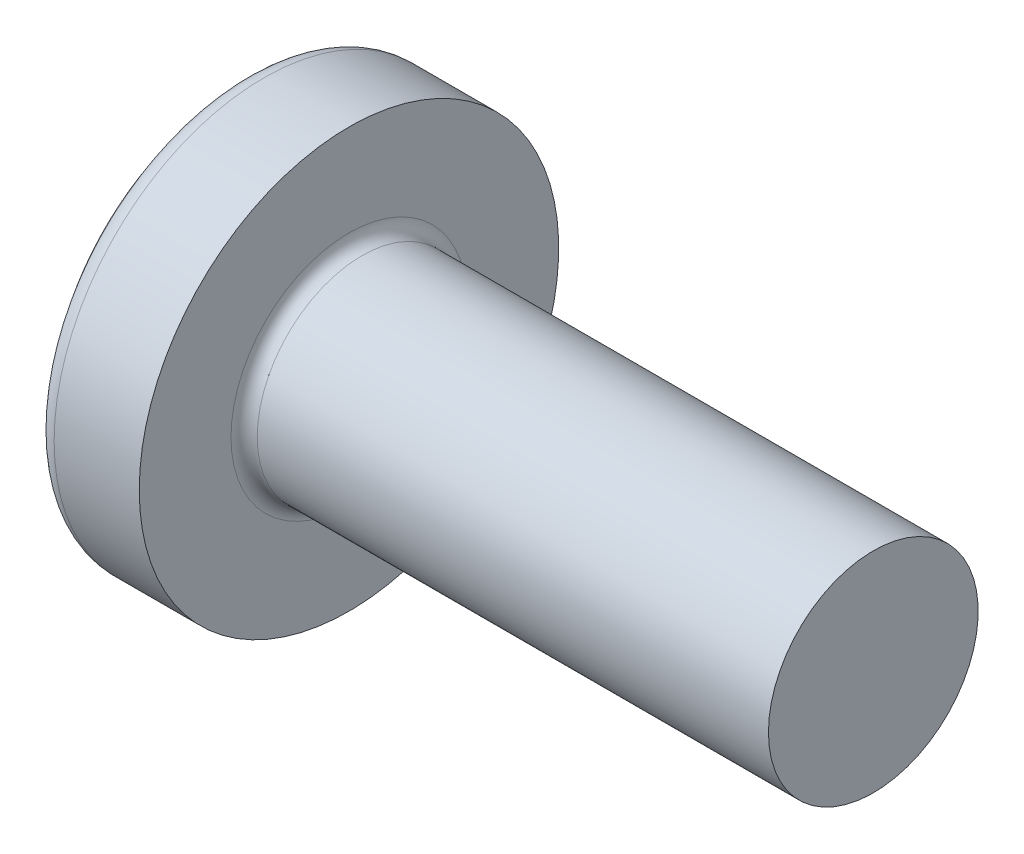
SolidWorks part; units mm, degrees
material "ABS"
ref_plane "Plane1" through (0, 0, 0) normal (0, 0, 1) x (1, 0, 0)
ref_plane "Plane2" through (0, 0, 0) normal (0, 1, 0) x (1, 0, 0)
ref_plane "Plane3" through (0, 0, 0) normal (1, 0, 0) x (0, 0, -1)
sketch "BodySke" plane through (0, 0, 0) normal (0, 0, 1) x (1, 0, 0)
  line L0 (1.3, 0.8) -> (1.3, 1.6)
  line L1 (1.475, 6.35) -> (1.475, -3.175) construction
  line L2 (-25.4, 0) -> (127, 0) construction
  line L3 (5.3, 0) -> (0, 0)
  line L4 (1.3, 0.8) -> (5.3, 0.8)
  line L5 (5.3, 0.8) -> (5.3, 0)
  line L6 (0.6507, 1.6) -> (1.3, 1.6)
  line L8 (1.3, 6.35) -> (1.3, -3.175) construction
  arc A0 (0.5326, 1.5426) -> (0, 0) centre (2.5, 0) ccw
  arc A2 (0.5326, 1.5426) -> (0.6507, 1.6) centre (0.6507, 1.45) cw
  dimension "Head_crown_rad" = 2.5
  dimension "Head_fillet_rad" = 0.15
  dimension "Length" = 4
  dimension "Head_ht" = 1.3
  dimension "Head_dia" = 3.2
  dimension "Advance" = 0.35
  dimension "Thread_nom" = 4
  dimension "Diameter" = 1.6
revolve "Base-Revolve" add sketch "BodySke"
cosmetic thread "ThreadCosmetic" [suppressed]
fillet "Fillet1" radius 0.1 1 edges at (1.3, 0, 0.8)
sketch "Sketch3" plane through (0, 0, 0) normal (1, 0, 0) x (0, 0, -1)
  line L0 (0.24, -0.8) -> (-0.24, -0.8)
  line L1 (0.24, -0.8) -> (0.24, 0.8)
  line L2 (-0.24, 0.8) -> (0.24, 0.8)
  line L3 (-0.24, 0.8) -> (-0.24, -0.8)
  dimension "Cross_dia" = 1.6
  dimension "D1" = 0.8
  dimension "Cross_width" = 0.48
  dimension "D2" = 0.24
ref_plane "Plane4" through (0.9, 0, 0) normal (1, 0, 0) x (0, 0, -1)
sketch "Sketch4" plane through (0.9, 0, 0) normal (1, 0, 0) x (0, 0, -1)
  line L0 (0.24, -0.3513) -> (-0.24, -0.3513)
  line L1 (0.24, -0.3513) -> (0.24, 0.3513)
  line L2 (-0.24, 0.3513) -> (0.24, 0.3513)
  line L3 (-0.24, 0.3513) -> (-0.24, -0.3513)
  dimension "D1" = 0.48
  dimension "D2" = 0.7026
  dimension "D3" = 0.24
  dimension "D4" = 0.3513
loft "Recess" cut profiles "Sketch3", "Sketch4"
pattern_circular "RecPat" count 2 every 90 about axis through (0, 0, 0) along (1, 0, 0) of "Recess"
sketch "RecCorSke" plane through (0, 0, 0) normal (0, 0, 1) x (1, 0, 0)
  line L0 (-3.175, 0) -> (15.875, 0) construction
  line L1 (-25.4, 0) -> (127, 0) construction
  line L2 (0, 0) -> (0, 0.4184)
  line L3 (0, 0.4184) -> (0.9, 0.3555)
  line L4 (0.9, 0.3555) -> (1.0155, 0)
  line L5 (1.0155, 0) -> (0, 0)
  dimension "Diameter" = 0.711
  dimension "Depth" = 0.9
  dimension "Draft_angle" = 4
  dimension "Bottom_angle" = 18
revolve "RecessCore" cut sketch "RecCorSke" angle 360 about L0
sketch "ThdSchSke" plane through (0, 0, 0) normal (0, 0, 1) x (1, 0, 0)
  line L0 (2, -0.601) -> (1.8607, -0.8)
  line L1 (2, -0.601) -> (2.1393, -0.8)
  line L2 (2.1393, -0.8) -> (2.1393, -1)
  line L3 (-3.175, 0) -> (5.1513, 0) construction
  line L5 (2.1393, -1) -> (1.8607, -1)
  line L6 (1.8607, -1) -> (1.8607, -0.8)
  dimension "Diameter" = 1.6
  dimension "SideAngle" = 55
  dimension "VeeAngle" = 70
  dimension "Thread_minor" = 1.202
  dimension "Overcut" = 2
  dimension "Start" = 2
revolve "ThreadSchematic" [suppressed] cut sketch "ThdSchSke" angle 360 about L3
pattern_linear "ThdSchPat" [suppressed]
equation "\"D1@Sketch3\" = \"Cross_dia@Sketch3\" / 2"
equation "\"D2@Sketch3\" = \"Cross_width@Sketch3\" / 2"
equation "\"Depth@RecCorSke\" = \"Cross_depth@Plane4\""
equation "\"D1@Sketch4\" = \"Cross_width@Sketch3\""
equation "\"D2@Sketch4\" = \"Cross_dia@Sketch3\" - 2.0 * \"Cross_depth@Plane4\" * tan(26.5  * 0.017453292)"
equation "\"D3@Sketch4\" = \"D1@Sketch4\" / 2"
equation "\"D4@Sketch4\" = \"D2@Sketch4\" / 2"
equation "\"Thread_length@ThreadCosmetic\" = ((sgn( (\"Length@BodySke\" - \"Advance@BodySke\" * 2.0 ) - \"Thread_nom@BodySke\" )-1)*( (\"Length@BodySke\" - \"Advance@BodySke\" * 2.0 ) - \"Thread_nom@BodySke\" ))/-2+ \"Thread_nom@BodySke\""
equation "\"Thread_minor@ThdSchSke\" = \"Thread_minor@ThreadCosmetic\""
equation "\"Diameter@ThdSchSke\" = \"Diameter@BodySke\""
equation "\"Overcut@ThdSchSke\" = \"Diameter@BodySke\" * 1.25"
equation "\"Start@ThdSchSke\" = \"Head_ht@BodySke\" + \"Length@BodySke\" - \"Thread_length@ThreadCosmetic\"  '---Non-countersunk---"
equation "\"Num_threads@ThdSchPat\" = int( \"Thread_length@ThreadCosmetic\" / \"Advance@BodySke\" + 0.999 )  + 1"
equation "\"Advance@ThdSchPat\" = \"Thread_length@ThreadCosmetic\" /  (\"Num_threads@ThdSchPat\" - 1) 'relax it"
